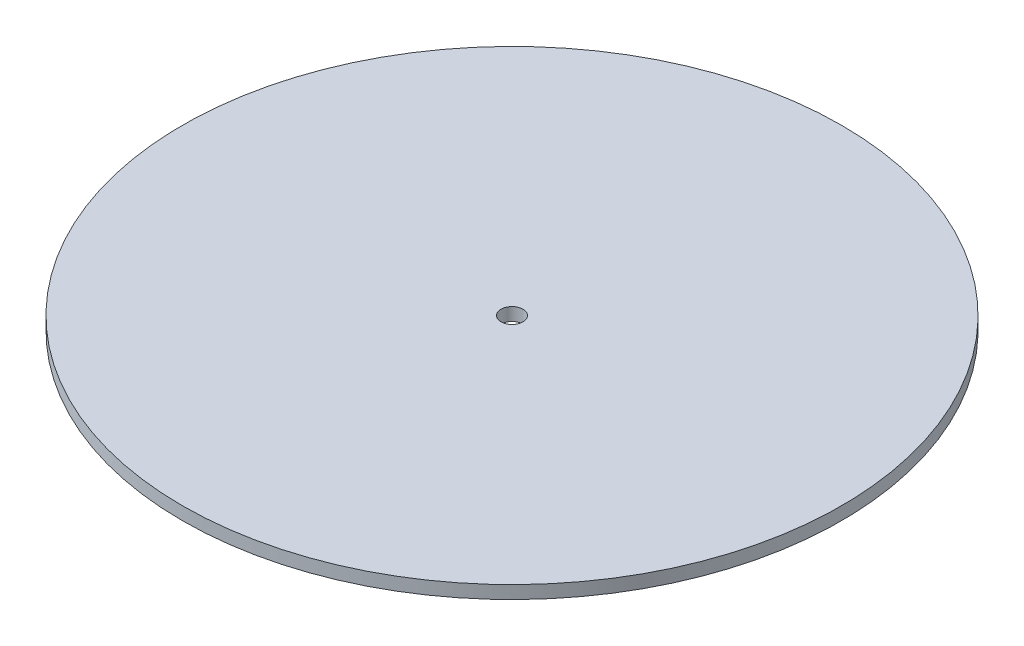
SolidWorks part; units mm, degrees
ref_plane "Front Plane" through (0, 0, 0) normal (0, 0, 1) x (1, 0, 0)
ref_plane "Top Plane" through (0, 0, 0) normal (0, 1, 0) x (1, 0, 0)
ref_plane "Right Plane" through (0, 0, 0) normal (1, 0, 0) x (0, 0, -1)
sketch "Sketch1" plane through (0, 0, 0) normal (0, 1, 0) x (1, 0, 0)
  circle A0 centre (0, 0) radius 76.2
  circle A1 centre (0, 0) radius 2.54
  dimension "D1" = 152.4
  dimension "D2" = 5.08
extrude "Boss-Extrude1" add sketch "Sketch1" along normal blind 3
